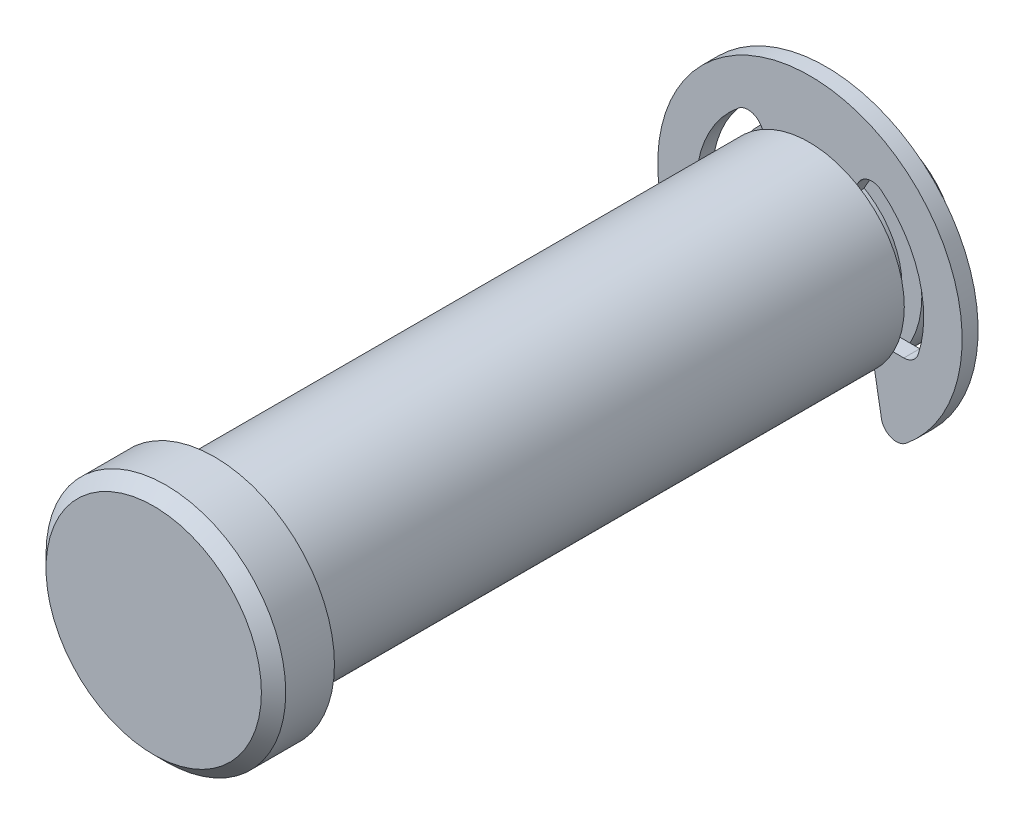
SolidWorks part; units mm, degrees
ref_plane "Front" through (0, 0, 0) normal (0, 0, 1) x (1, 0, 0)
ref_plane "Top" through (0, 0, 0) normal (0, 1, 0) x (1, 0, 0)
ref_plane "Right" through (0, 0, 0) normal (1, 0, 0) x (0, 0, -1)
sketch "Sketch2" plane through (0, 0, 0) normal (0, 0, 1) x (1, 0, 0)
  circle A0 centre (0, 0) radius 6.35
  point P3 (0, 6.35)
  point P4 (0, -6.35)
  dimension "dia" = 12.7
extrude "Extrude1" add sketch "Sketch2" along normal mid plane 44.45
sketch "Sketch3" plane through (0, 0, 0) normal (1, 0, 0) x (0, 0, -1)
  line L0 (22.225, 6.35) -> (-22.225, 6.35) construction
  line L1 (17.4625, 6.35) -> (18.6309, 6.35)
  line L2 (17.4625, 6.35) -> (17.4625, 5.0292)
  line L3 (17.4625, 5.0292) -> (18.6309, 5.0292)
  line L4 (18.6309, 6.35) -> (18.6309, 5.0292)
  line L5 (-22.225, 6.35) -> (-22.225, -6.35) construction
  line L10 (18.6309, 5.0292) -> (18.6309, -5.0292) construction
  point P11 (18.6309, 0)
  point P14 (18.0467, 6.35)
  dimension "groove wd" = 1.1684
  dimension "groove dia" = 10.0584
  dimension "usable lg" = 39.6875
revolve "Cut-Revolve1" cut sketch "Sketch3" angle 360 about axis through (0, 0, 22.225) along (0, 0, -1)
sketch "Sketch8" plane through (0, 0, 22.225) normal (0, 0, 1) x (1, 0, 0)
  circle A0 centre (0, 0) radius 8.001
  dimension "head dia" = 16.002
extrude "Extrude6" add sketch "Sketch8" along normal blind 4.064
chamfer "Chamfer2" distance 0.8128 angle 45 1 edges at (8.001, 0, 26.289)
ref_plane "Plane1" through (0, 0, -18.0467) normal (0, 0, 1) x (1, 0, 0)
sketch "Sketch4" plane through (0, 0, -18.0467) normal (0, 0, 1) x (1, 0, 0)
  line L0 (0, 5.0292) -> (0, -5.0292) construction
  circle A0 centre (0, 0) radius 10.16
  circle A1 centre (0, 0) radius 5.0292
  dimension "ring dia" = 20.32
extrude "Extrude2" add sketch "Sketch4" along normal mid plane 1.0668 separate body
sketch "Sketch5" plane through (0, 0, 0) normal (0, 0, 1) x (1, 0, 0)
  line L0 (0, 10.16) -> (0, 5.0292) construction
  line L1 (-3.7973, 6.5771) -> (0, 0)
  line L2 (-6.9694, -3.0175) -> (-4.0234, -3.0175)
  line L3 (0, 0) -> (3.7973, 6.5771)
  line L4 (-4.0234, -3.0175) -> (-5.0462, -8.8183)
  line L5 (4.0234, -3.0175) -> (5.0462, -8.8183)
  line L6 (4.0234, -3.0175) -> (6.9694, -3.0175)
  arc A0 (-3.7973, 6.5771) -> (-6.9694, -3.0175) centre (0, 0) ccw
  circle A1 centre (0, 0) radius 10.16 construction
  circle A2 centre (0, 0) radius 5.0292 construction
  arc A3 (6.9694, -3.0175) -> (3.7973, 6.5771) centre (0, 0) ccw
  arc A4 (-5.0462, -8.8183) -> (5.0462, -8.8183) centre (0, 0) ccw
  circle A5 centre (0, 0) radius 5.0292 construction
  point P10 (0, 7.5946)
  dimension "D1" = 30
  dimension "D2" = 10
  dimension "D3" = 3.0175
extrude "Extrude4" cut sketch "Sketch5" against normal through all
sketch "Sketch6" plane through (0, 0, -17.5133) normal (0, 0, 1) x (1, 0, 0)
  line L0 (-2.5146, 4.3554) -> (2.5146, 4.3554)
  circle A0 centre (0, 0) radius 5.0292 construction
  arc A1 (2.5146, 4.3554) -> (-2.5146, 4.3554) centre (0, 0) ccw
extrude "Extrude5" add sketch "Sketch6" against normal up to surface (1.0668 mm away) up to face at (0, 1.3019, -18.5801)
fillet "Fillet1" radius 1.016 6 edges at (5.0462, -8.8183, -18.0467) (-5.0462, -8.8183, -18.0467) (6.9694, -3.0175, -18.0467) (3.7973, 6.5771, -18.0467) (-3.7973, 6.5771, -18.0467) (-6.9694, -3.0175, -18.0467)
chamfer "Chamfer1" distance 1.27 angle 45 1 edges at (6.35, 0, -22.225)
sketch "Sketch7" plane through (0, 0, 0) normal (1, 0, 0) x (0, 0, -1)
  line L0 (18.5801, 10.16) -> (17.5133, 10.16) construction
  line L1 (22.225, -6.35) -> (22.225, 6.35) construction
  line L2 (17.5133, -8.107) -> (18.5801, -8.107) construction
  line L3 (-26.289, 7.1882) -> (-26.289, -7.1882) construction
  point P0 (18.6309, -8.107)
  point P1 (22.225, 6.35)
  point P2 (-26.289, 8.001)
  point P6 (17.4625, 10.16)
  point P7 (22.225, -6.35)
  point P12 (-22.225, 8.001)
  point P16 (17.4625, -8.107)
equation "\"D1@Chamfer1\" = \"dia@Sketch2\" * .1"
equation "\"D1@Fillet1\" = \"ring dia@Sketch4\" * .05"
equation "\"D3@Sketch5\" = \"groove dia@Sketch3\" * .3"
equation "\"D1@Chamfer2\" = \"head ht@Extrude6\" * .2"
